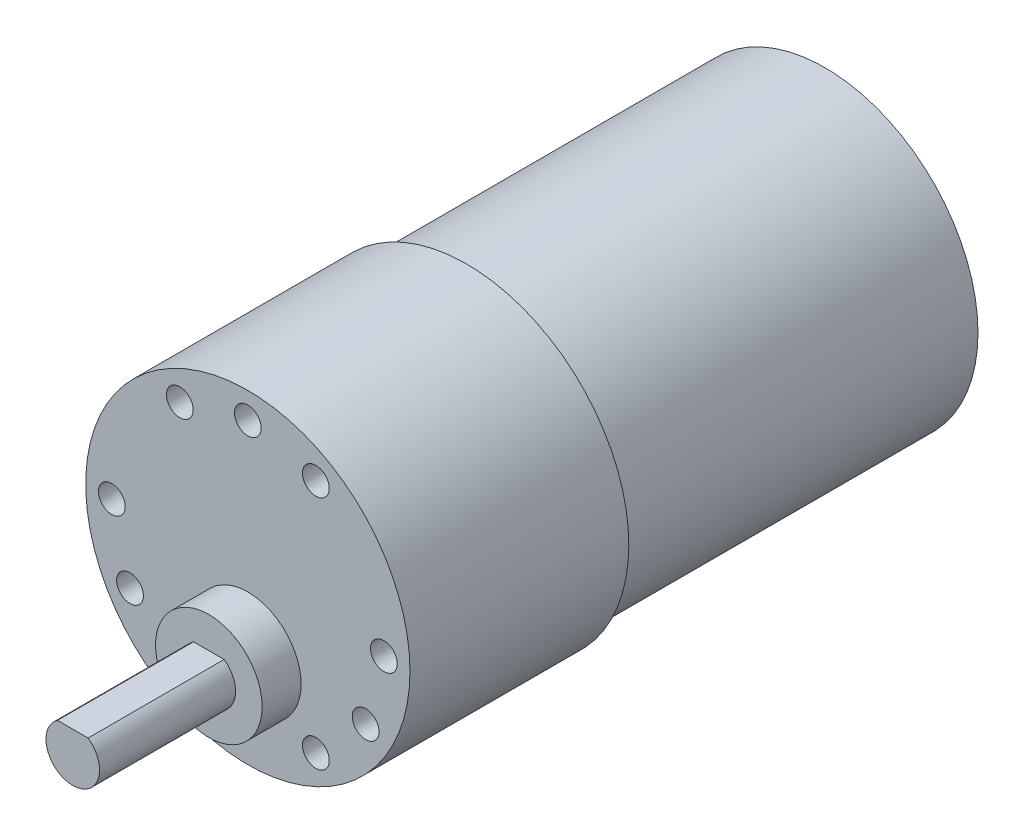
SolidWorks part; units mm, degrees
ref_plane "Front Plane" through (0, 0, 0) normal (0, 0, 1) x (1, 0, 0)
ref_plane "Top Plane" through (0, 0, 0) normal (0, 1, 0) x (1, 0, 0)
ref_plane "Right Plane" through (0, 0, 0) normal (1, 0, 0) x (0, 0, -1)
sketch "Sketch1" plane through (0, 0, 0) normal (0, 0, 1) x (1, 0, 0)
  circle A0 centre (0, 0) radius 18.161
  dimension "D1" = 36.322
extrude "Boss-Extrude1" add sketch "Sketch1" along normal blind 24.511
sketch "Sketch5" plane through (0, 0, 24.511) normal (0, 0, 1) x (1, 0, 0)
  circle A0 centre (0, -7.366) radius 5.969
  dimension "D1" = 11.938
  dimension "D2" = 7.366
extrude "Boss-Extrude5" add sketch "Sketch5" along normal blind 4.3688
sketch "Sketch6" plane through (0, 0, 28.8798) normal (0, 0, 1) x (1, 0, 0)
  line L0 (-1.7157, -4.905) -> (1.7157, -4.905)
  arc A0 (-1.7157, -4.905) -> (1.7157, -4.905) centre (0, -7.366) ccw
  dimension "D1" = 6
  dimension "D2" = 2.461
extrude "Boss-Extrude6" add sketch "Sketch6" along normal blind 15.24
sketch "Sketch9" plane through (0, 0, 24.511) normal (0, 0, 1) x (1, 0, 0)
  line L0 (0, 0) -> (0, 15.24) construction
  circle A0 centre (0, 0) radius 15.24 construction
  dimension "D1" = 30.48
hole_wizard "Ø3.0mm Dowel Hole1" positions "Sketch11" profile "Sketch12" hole size "Ø3.0" standard "ANSI Metric"
sketch "Sketch11" plane through (0, 0, 24.511) normal (0, 0, 1) x (1, 0, 0)
  point P0 (0, 15.24)
sketch "Sketch12" plane through (0, 15.24, 24.511) normal (1, 0, 0) x (0, -1, 0)
  line L0 (0, 0) -> (0, 11.0613)
  line L1 (0, 11.0613) -> (1.5, 10.16)
  line L2 (1.5, 10.16) -> (1.5, 0)
  line L5 (1.5, 0) -> (0, 0)
  line L10 (0, 11.0613) -> (-1.5, 10.16) construction
  line L11 (0, -6.35) -> (0, 107.95) construction
  dimension "Hole Dia." = 3
  dimension "Hole Depth" = 10.16
  dimension "Drill Angle" = 118
pattern_circular "CirPattern2" count 12 over 360 about axis through (0, 0, 0) along (0, 0, 1) skipping 2, 6, 10 of "Ø3.0mm Dowel Hole1"
sketch "Sketch2" plane through (0, 0, 0) normal (0, 0, -1) x (-1, 0, 0)
  circle A0 centre (0, 0) radius 17.145
  dimension "D1" = 34.29
extrude "Boss-Extrude2" add sketch "Sketch2" along normal blind 40.132
sketch "Sketch3" plane through (0, 0, -40.132) normal (0, 0, -1) x (-1, 0, 0)
  circle A0 centre (0, 0) radius 3.048
  dimension "D1" = 6.096
extrude "Boss-Extrude3" add sketch "Sketch3" along normal blind 3.81
sketch "Sketch13" plane through (0, 0, -40.132) normal (0, 0, -1) x (-1, 0, 0)
  circle A0 centre (0, 0) radius 16.637
  dimension "D1" = 33.274
extrude "Cut-Extrude1" cut sketch "Sketch13" against normal blind 1.016
sketch "Sketch14" plane through (0, 0, -39.116) normal (0, 0, -1) x (-1, 0, 0)
  line L0 (0, 0) -> (2.9583, -11.0405) construction
  line L1 (0, 0) -> (-6.5307, -7.783) construction
  circle A0 centre (0, 0) radius 11.43 construction
  circle A1 centre (0, 0) radius 10.16 construction
  dimension "D1" = 22.86
  dimension "D2" = 20.32
ref_plane "Plane1" through (0, 0, 0) normal (0.766, 0.6428, 0) x (0.6428, -0.766, 0)
ref_plane "Plane2" through (0, 0, 0) normal (0.9659, -0.2588, 0) x (-0.2588, -0.9659, 0)
sketch "Sketch15" plane through (0, 0, 0) normal (0.766, 0.6428, 0) x (0.6428, -0.766, 0)
  line L0 (8.89, 39.116) -> (8.89, 44.196)
  line L3 (10.16, 39.116) -> (-10.16, 39.116) construction
  line L4 (8.89, 44.196) -> (11.43, 44.196)
  line L5 (11.43, 44.196) -> (11.43, 39.116)
  line L6 (11.43, 39.116) -> (-11.43, 39.116) construction
  line L7 (11.43, 39.116) -> (8.89, 39.116)
  circle A0 centre (10.16, 42.926) radius 0.4445
  dimension "D4" = 0.889
  dimension "D1" = 5.08
  dimension "D2" = 2.54
  dimension "D3" = 1.27
  dimension "D5" = 1.27
  dimension "D6" = 1.27
extrude "Boss-Extrude7" add sketch "Sketch15" along normal mid plane 0.508
sketch "Sketch16" plane through (0, 0, 0) normal (0.9659, -0.2588, 0) x (-0.2588, -0.9659, 0)
  line L0 (12.7, 39.116) -> (12.7, 44.196)
  line L1 (12.7, 44.196) -> (10.16, 44.196)
  line L2 (10.16, 44.196) -> (10.16, 39.116)
  line L3 (10.16, 39.116) -> (-10.16, 39.116) construction
  line L4 (10.16, 39.116) -> (12.7, 39.116)
  circle A0 centre (11.43, 42.926) radius 0.6786
  point P11 (11.8197, 44.196)
  dimension "D1" = 1.27
  dimension "D2" = 2.54
  dimension "D3" = 5.08
  dimension "D4" = 1.27
  dimension "D5" = 1.27
extrude "Boss-Extrude8" add sketch "Sketch16" along normal mid plane 0.508
